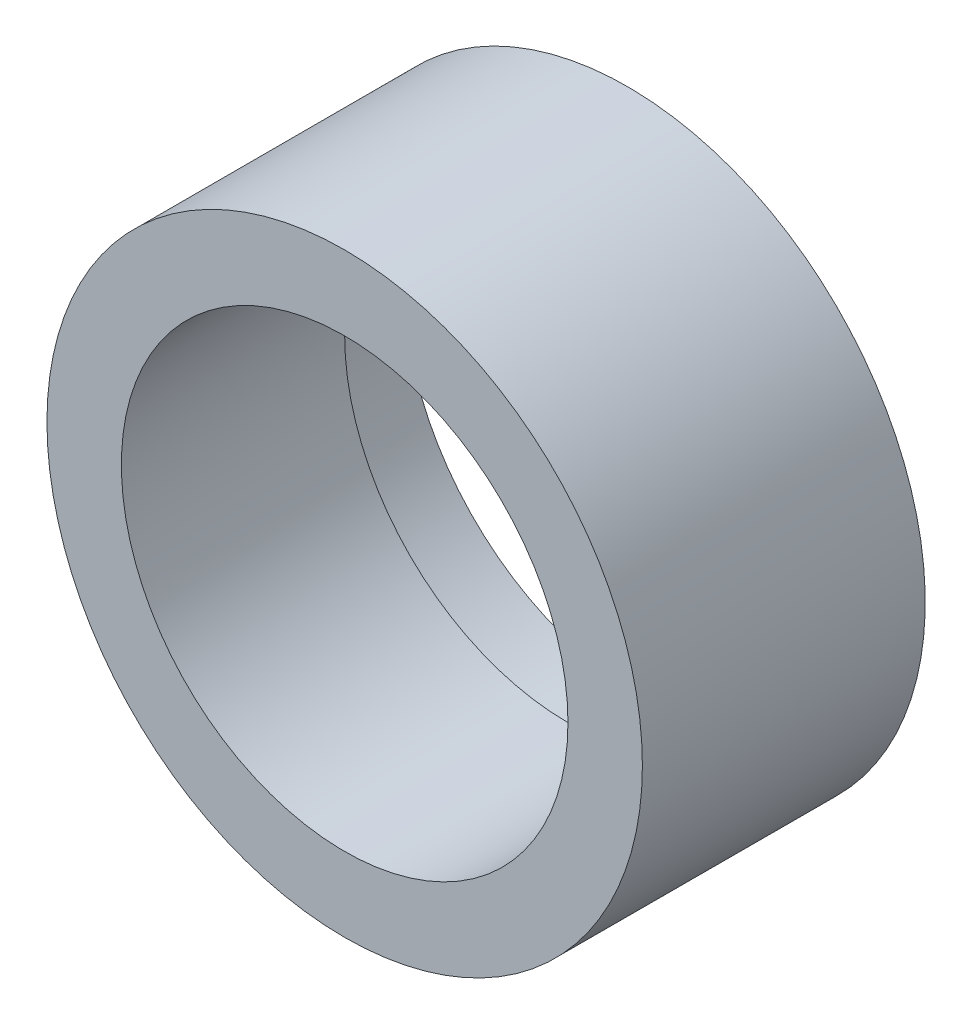
SolidWorks part; units mm, degrees
material "2024 合金"
ref_plane "正面" through (0, 0, 0) normal (0, 0, 1) x (1, 0, 0)
ref_plane "平面" through (0, 0, 0) normal (0, 1, 0) x (1, 0, 0)
ref_plane "右側面" through (0, 0, 0) normal (1, 0, 0) x (0, 0, -1)
sketch "ｽｹｯﾁ1" plane through (0, 0, 0) normal (0, 0, 1) x (1, 0, 0)
  circle A0 centre (0, 0) radius 20
  dimension "D1" = 40
extrude "ﾎﾞｽ - 押し出し1" add sketch "ｽｹｯﾁ1" along normal blind 20
sketch "ｽｹｯﾁ4" plane through (0, 0, 0) normal (0, 0, -1) x (-1, 0, 0)
  circle A0 centre (0, 0) radius 20
  circle A1 centre (0, 0) radius 18.5
  dimension "D1" = 40
  dimension "D2" = 37
extrude "ｶｯﾄ - 押し出し3" cut sketch "ｽｹｯﾁ4" against normal blind 1
sketch "ｽｹｯﾁ3" plane through (0, 0, 0) normal (0, 0, -1) x (-1, 0, 0)
  circle A0 centre (0, 0) radius 16
  dimension "D1" = 32
extrude "ｶｯﾄ - 押し出し2" cut sketch "ｽｹｯﾁ3" against normal blind 5
ref_plane "平面2" through (0, 0, 5) normal (0, 0, -1) x (-1, 0, 0)
sketch "ｽｹｯﾁ6" plane through (0, 0, 20) normal (0, 0, 1) x (1, 0, 0)
  circle A0 centre (0, 0) radius 15
  dimension "D1" = 30
extrude "ｶｯﾄ - 押し出し4" cut sketch "ｽｹｯﾁ6" against normal through all
